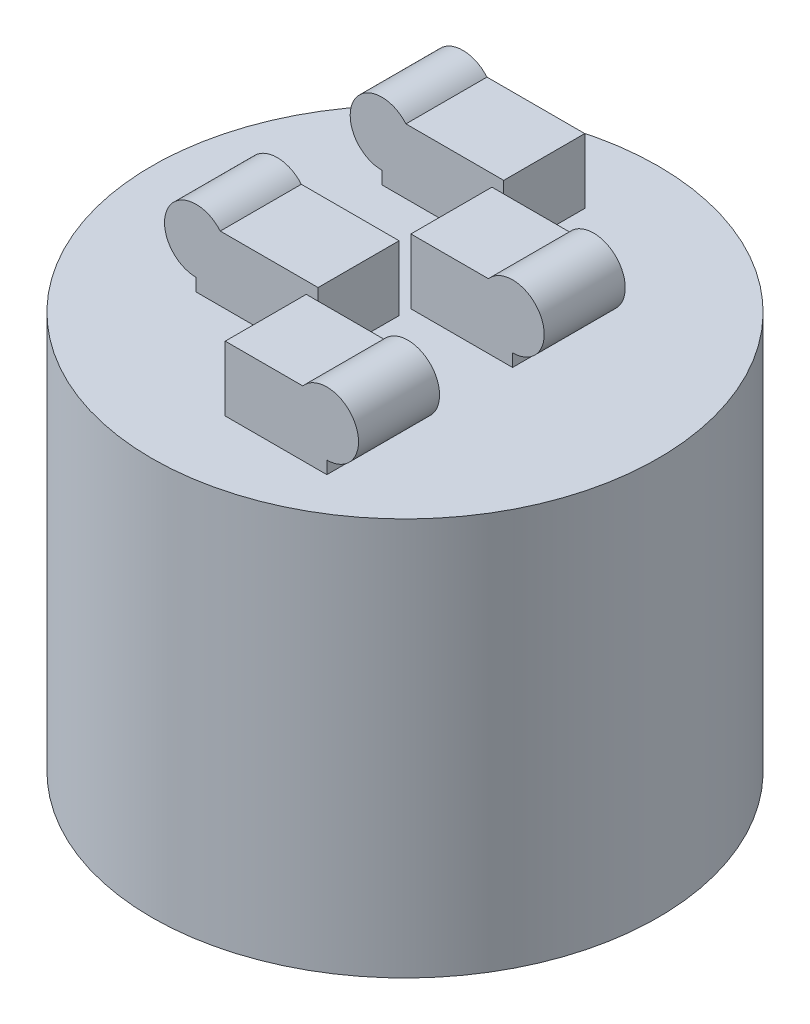
SolidWorks part; units mm, degrees
ref_plane "Front Plane" through (0, 0, 0) normal (0, 0, 1) x (1, 0, 0)
ref_plane "Top Plane" through (0, 0, 0) normal (0, 1, 0) x (1, 0, 0)
ref_plane "Right Plane" through (0, 0, 0) normal (1, 0, 0) x (0, 0, -1)
sketch "Sketch1" plane through (0, 0, 0) normal (0, 1, 0) x (1, 0, 0)
  circle A0 centre (0, 0) radius 50
  dimension "D1" = 100
extrude "Boss-Extrude1" add sketch "Sketch1" along normal blind 78.5
ref_plane "Plane1" through (0, 0, 9.165) normal (0, 0, 1) x (1, 0, 0)
ref_plane "Plane2" through (0, 0, 27.495) normal (0, 0, 1) x (1, 0, 0)
sketch "Sketch2" plane through (0, 0, 9.165) normal (0, 0, 1) x (1, 0, 0)
  line L0 (-14.9118, 87.25) -> (49985.0882, 87.25) construction
  line L1 (50, 78.5) -> (-50, 78.5) construction
  line L2 (-77.3581, 72.5) -> (49922.6419, 72.5) construction
  line L3 (-87.0616, 91.3) -> (49912.9384, 91.3) construction
  line L4 (-24.07, 81) -> (-24.07, 91.3) construction
  line L5 (0, 78.5) -> (-24.07, 78.5)
  line L6 (0, 78.5) -> (0, 91.3)
  line L7 (0, 91.3) -> (-19.3097, 91.3)
  line L8 (-24.07, 78.5) -> (-24.07, 81)
  arc A0 (-19.3097, 91.3) -> (-24.07, 81) centre (-24.07, 87.25) ccw
  circle A1 centre (-24.07, 87.25) radius 1.5 construction
  dimension "D5" = 12.5
  dimension "D6" = 3
  dimension "D1" = 8.75
  dimension "D2" = 14.75
  dimension "D3" = 18.8
  dimension "D4" = 24.07
extrude "Boss-Extrude2" add sketch "Sketch2" along normal mid plane 16
pattern_linear "LPattern1" count 2 spacing 36.66 along (0, 0, -1) of "Boss-Extrude2"
sketch "Sketch3" plane through (0, 0, 27.495) normal (0, 0, 1) x (1, 0, 0)
  line L0 (-28.3187, 72.5) -> (49971.6813, 72.5) construction
  line L1 (10.787, 87.25) -> (50010.787, 87.25) construction
  line L2 (9.7083, 91.3) -> (50009.7083, 91.3) construction
  line L3 (50, 78.5) -> (-50, 78.5) construction
  line L4 (0, 91.3) -> (15.3097, 91.3)
  line L5 (0, 78.5) -> (20.07, 78.5)
  line L6 (0, 78.5) -> (0, 91.3)
  line L7 (0, 91.3) -> (20.07, 91.3) construction
  line L8 (20.07, 78.5) -> (20.07, 91.3) construction
  line L9 (20.07, 78.5) -> (20.07, 81)
  circle A0 centre (20.07, 87.25) radius 6.25 construction
  arc A1 (15.3097, 91.3) -> (20.07, 81) centre (20.07, 87.25) cw
  dimension "D5" = 12.5
  dimension "D1" = 8.75
  dimension "D2" = 14.75
  dimension "D3" = 18.8
  dimension "D4" = 20.07
extrude "Boss-Extrude3" add sketch "Sketch3" along normal mid plane 16
pattern_linear "LPattern2" count 2 spacing 36.66 along (0, 0, -1) of "Boss-Extrude3"
